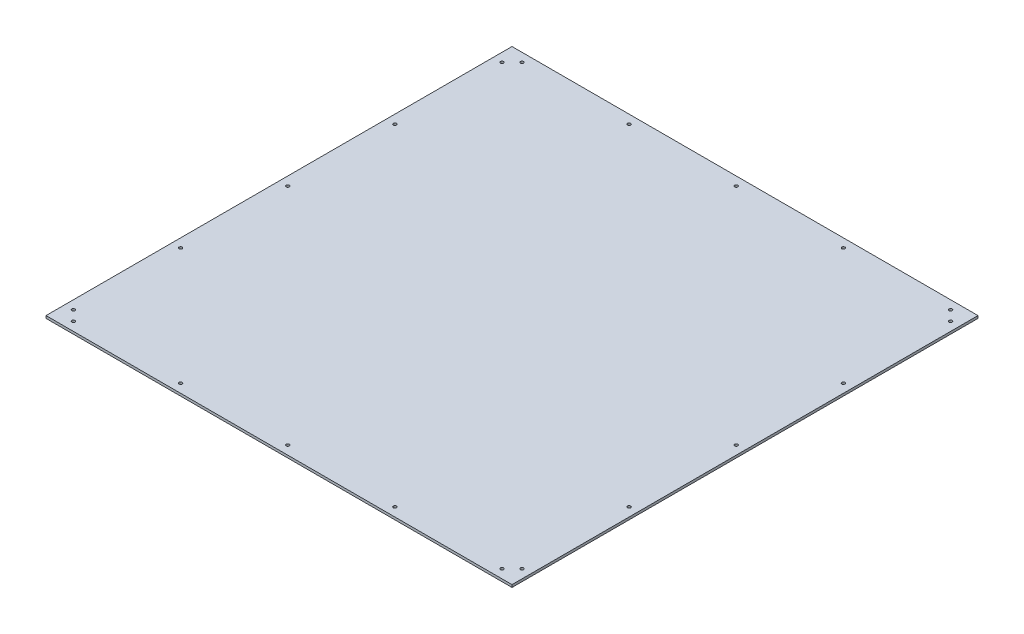
SolidWorks part; units mm, degrees
ref_plane "Front Plane" through (0, 0, 0) normal (0, 0, 1) x (1, 0, 0)
ref_plane "Top Plane" through (0, 0, 0) normal (0, 1, 0) x (1, 0, 0)
ref_plane "Right Plane" through (0, 0, 0) normal (1, 0, 0) x (0, 0, -1)
sketch "Sketch1" plane through (0, 0, 0) normal (0, 1, 0) x (1, 0, 0)
  line L0 (0, 374) -> (0, -374) construction
  line L1 (-374, -374) -> (374, -374)
  line L2 (-374, -374) -> (-374, 374)
  line L3 (-374, 374) -> (374, 374)
  line L4 (374, -374) -> (374, 374)
  line L5 (-374, -374) -> (374, 374) construction
  line L6 (-374, 374) -> (374, -374) construction
  line L7 (-374, 0) -> (374, 0) construction
  line L8 (-344, 360) -> (0, 360) construction
  circle A0 centre (-344, 360) radius 2.5
  circle A1 centre (0, 360) radius 2.5
  circle A6 centre (-172, 360) radius 2.5
  circle A7 centre (-360, 0) radius 2.5
  circle A8 centre (-360, 172) radius 2.5
  circle A9 centre (-360, 344) radius 2.5
  circle A10 centre (360, 0) radius 2.5
  circle A11 centre (172, 360) radius 2.5
  circle A12 centre (360, 344) radius 2.5
  circle A13 centre (360, 172) radius 2.5
  circle A14 centre (344, 360) radius 2.5
  circle A15 centre (360, -172) radius 2.5
  circle A16 centre (360, -344) radius 2.5
  circle A17 centre (344, -360) radius 2.5
  circle A18 centre (172, -360) radius 2.5
  circle A19 centre (0, -360) radius 2.5
  circle A20 centre (-172, -360) radius 2.5
  circle A21 centre (-344, -360) radius 2.5
  circle A22 centre (-360, -344) radius 2.5
  circle A23 centre (-360, -172) radius 2.5
  point P0 (0, 0)
  point P17 (-172, 360)
  point P26 (360, 172)
  point P27 (360, 344)
  dimension "D3" = 5
  dimension "D4" = 5
  dimension "D7" = 30
  dimension "D1" = 5
  dimension "748" = 748
  dimension "D2" = 748
  dimension "D5" = 14
  dimension "D6" = 14
extrude "Boss-Extrude1" add sketch "Sketch1" along normal blind 4
